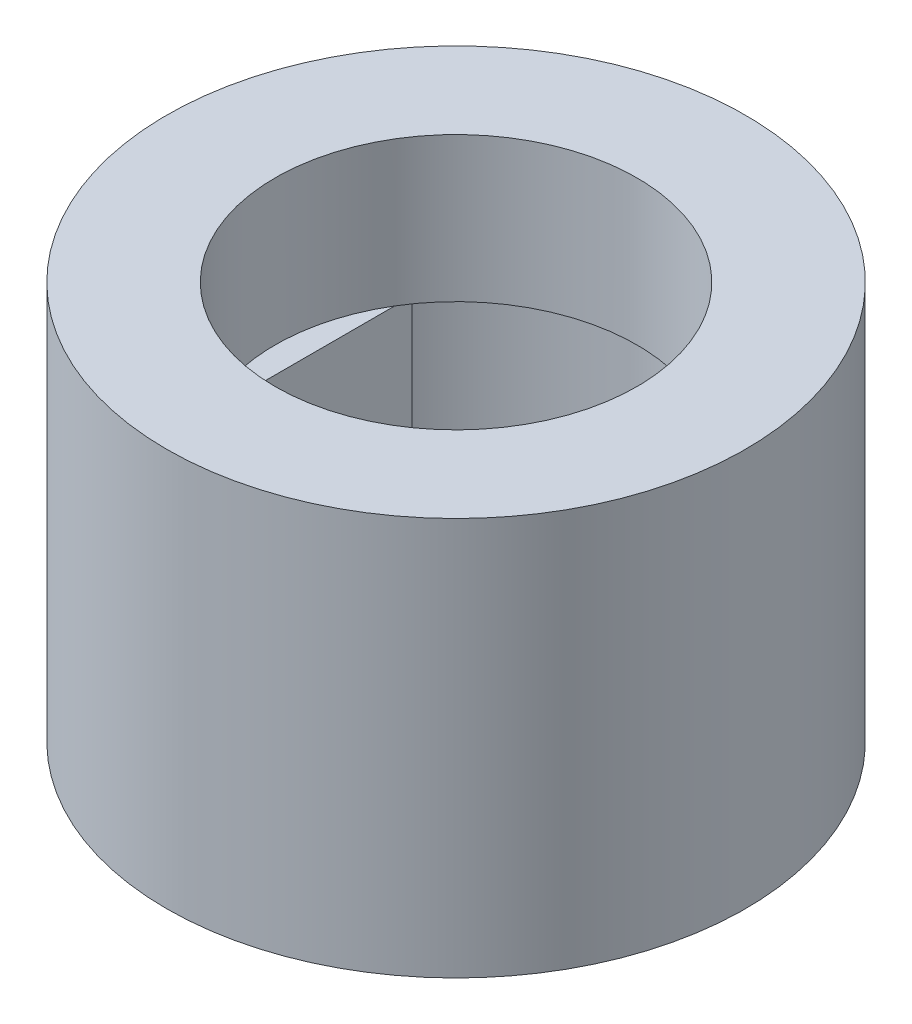
SolidWorks part; units mm, degrees
ref_plane "Front Plane" through (0, 0, 0) normal (0, 0, 1) x (1, 0, 0)
ref_plane "Top Plane" through (0, 0, 0) normal (0, 1, 0) x (1, 0, 0)
ref_plane "Right Plane" through (0, 0, 0) normal (1, 0, 0) x (0, 0, -1)
sketch "Sketch1" plane through (0, 0, 0) normal (0, 1, 0) x (1, 0, 0)
  circle A0 centre (0, 0) radius 5.08
  dimension "D1" = 10.16
extrude "Boss-Extrude1" add sketch "Sketch1" along normal blind 6.985
sketch "Sketch2" plane through (0, 0, 0) normal (0, 1, 0) x (1, 0, 0)
  line L0 (-2.7178, -1.9416) -> (-2.7178, 1.9416)
  line L1 (0, 0) -> (-2.7178, 0) construction
  circle A0 centre (0, 0) radius 3.3401
  dimension "D1" = 6.6802
  dimension "D2" = 2.7178
extrude "Cut-Extrude1" cut sketch "Sketch2" along normal blind 4.445
sketch "Sketch3" plane through (0, 6.985, 0) normal (0, 1, 0) x (1, 0, 0)
  circle A0 centre (0, 0) radius 3.175
  dimension "D1" = 6.35
extrude "Cut-Extrude2" cut sketch "Sketch3" against normal blind 2.54
